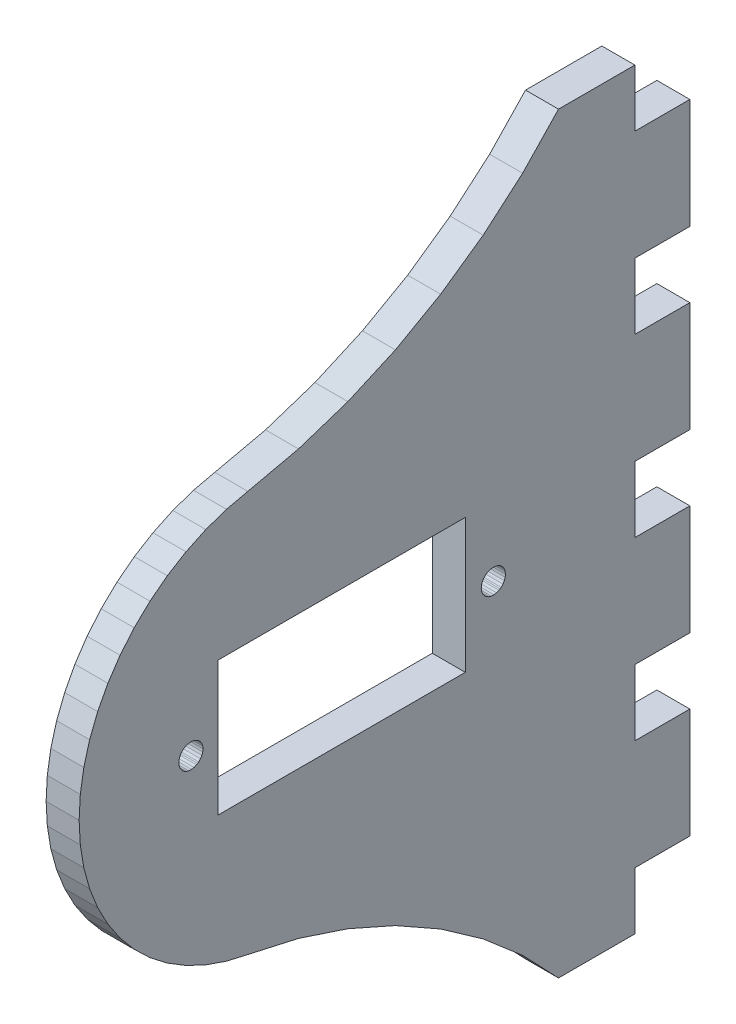
SolidWorks part; units mm, degrees
ref_plane "Front Plane" through (0, 0, 0) normal (0, 0, 1) x (1, 0, 0)
ref_plane "Top Plane" through (0, 0, 0) normal (0, 1, 0) x (1, 0, 0)
ref_plane "Right Plane" through (0, 0, 0) normal (1, 0, 0) x (0, 0, -1)
ref_plane "Plane1" through (3, 0, 0) normal (1, 0, 0) x (0, 0, -1)
sketch "Sketch1" plane through (3, 0, 0) normal (1, 0, 0) x (0, 0, -1)
  line L0 (-21.3207, 14.0362) -> (-22.7581, 12.6593)
  line L1 (-22.7581, 12.6593) -> (-24.0394, 11.136)
  line L2 (-24.0394, 11.136) -> (-25.1497, 9.4839)
  line L3 (-25.1497, 9.4839) -> (-26.0762, 7.7222)
  line L4 (-26.0762, 7.7222) -> (-26.8081, 5.8712)
  line L5 (-26.8081, 5.8712) -> (-27.3371, 3.9522)
  line L6 (-27.3371, 3.9522) -> (-27.6569, 1.9876)
  line L7 (-27.6569, 1.9876) -> (-27.7639, 0)
  line L8 (-27.7639, 0) -> (-27.6569, -1.9876)
  line L9 (-27.6569, -1.9876) -> (-27.3371, -3.9522)
  line L10 (-27.3371, -3.9522) -> (-26.8081, -5.8712)
  line L11 (-26.8081, -5.8712) -> (-26.0762, -7.7222)
  line L12 (-26.0762, -7.7222) -> (-25.1497, -9.4839)
  line L13 (-25.1497, -9.4839) -> (-24.0394, -11.136)
  line L14 (-24.0394, -11.136) -> (-22.7581, -12.6593)
  line L15 (-22.7581, -12.6593) -> (-21.3207, -14.0362)
  line L16 (-21.3207, -14.0362) -> (-19.7437, -15.2508)
  line L17 (-19.7437, -15.2508) -> (-18.0454, -16.289)
  line L18 (-18.0454, -16.289) -> (-16.2454, -17.1388)
  line L19 (-16.2454, -17.1388) -> (-14.3646, -17.7905)
  line L20 (-14.3646, -17.7905) -> (-12.4247, -18.2364)
  line L21 (-12.4247, -18.2364) -> (-7.8143, -19.2726)
  line L22 (-7.8143, -19.2726) -> (-3.3272, -20.7541)
  line L23 (-3.3272, -20.7541) -> (0.9938, -22.6669)
  line L24 (0.9938, -22.6669) -> (5.1073, -24.9927)
  line L25 (5.1073, -24.9927) -> (8.9739, -27.7091)
  line L26 (8.9739, -27.7091) -> (12.5566, -30.7902)
  line L27 (12.5566, -30.7902) -> (15.8213, -34.2066)
  line L28 (15.8213, -34.2066) -> (22.7639, -34.2066)
  line L29 (22.7639, -34.2066) -> (22.7639, -28.9999)
  line L30 (22.7639, -28.9999) -> (27.7639, -28.9999)
  line L31 (27.7639, -28.9999) -> (27.7639, -18.9999)
  line L32 (27.7639, -18.9999) -> (22.7639, -18.9999)
  line L33 (22.7639, -18.9999) -> (22.7639, -12.9999)
  line L34 (22.7639, -12.9999) -> (27.7639, -12.9999)
  line L35 (27.7639, -12.9999) -> (27.7639, -2.9999)
  line L36 (27.7639, -2.9999) -> (22.7639, -2.9999)
  line L37 (22.7639, -2.9999) -> (22.7639, 3.0001)
  line L38 (22.7639, 3.0001) -> (27.7639, 3.0001)
  line L39 (27.7639, 3.0001) -> (27.7639, 13.0001)
  line L40 (27.7639, 13.0001) -> (22.7639, 13.0001)
  line L41 (22.7639, 13.0001) -> (22.7639, 19.0001)
  line L42 (22.7639, 19.0001) -> (27.7639, 19.0001)
  line L43 (27.7639, 19.0001) -> (27.7639, 29.0001)
  line L44 (27.7639, 29.0001) -> (22.7639, 29.0001)
  line L45 (22.7639, 29.0001) -> (22.7639, 34.2066)
  line L46 (22.7639, 34.2066) -> (15.8213, 34.2066)
  line L47 (15.8213, 34.2066) -> (12.5566, 30.7902)
  line L48 (12.5566, 30.7902) -> (8.9739, 27.7091)
  line L49 (8.9739, 27.7091) -> (5.1073, 24.9927)
  line L50 (5.1073, 24.9927) -> (0.9938, 22.6669)
  line L51 (0.9938, 22.6669) -> (-3.3272, 20.7541)
  line L52 (-3.3272, 20.7541) -> (-7.8143, 19.2726)
  line L53 (-7.8143, 19.2726) -> (-12.4247, 18.2364)
  line L54 (-12.4247, 18.2364) -> (-14.3646, 17.7905)
  line L55 (-14.3646, 17.7905) -> (-16.2454, 17.1388)
  line L56 (-16.2454, 17.1388) -> (-18.0454, 16.289)
  line L57 (-18.0454, 16.289) -> (-19.7437, 15.2508)
  line L58 (-19.7437, 15.2508) -> (-21.3207, 14.0362)
  line L59 (7.3461, -5.9) -> (-15.1539, -5.9)
  line L60 (-15.1539, -5.9) -> (-15.1539, 6.3)
  line L61 (-15.1539, 6.3) -> (7.3461, 6.3)
  line L62 (7.3461, 6.3) -> (7.3461, -5.9)
  line L63 (-18.1192, 0.9719) -> (-17.8982, 1.0599)
  line L64 (-17.8982, 1.0599) -> (-17.6635, 1.0984)
  line L65 (-17.6635, 1.0984) -> (-17.426, 1.0855)
  line L66 (-17.426, 1.0855) -> (-17.1968, 1.0219)
  line L67 (-17.1968, 1.0219) -> (-16.9866, 0.9105)
  line L68 (-16.9866, 0.9105) -> (-16.8918, 0.8384)
  line L69 (-16.8918, 0.8384) -> (-16.7282, 0.6657)
  line L70 (-16.7282, 0.6657) -> (-16.6056, 0.4619)
  line L71 (-16.6056, 0.4619) -> (-16.5296, 0.2365)
  line L72 (-16.5296, 0.2365) -> (-16.5039, 0)
  line L73 (-16.5039, 0) -> (-16.5296, -0.2365)
  line L74 (-16.5296, -0.2365) -> (-16.6056, -0.4619)
  line L75 (-16.6056, -0.4619) -> (-16.7282, -0.6657)
  line L76 (-16.7282, -0.6657) -> (-16.8918, -0.8384)
  line L77 (-16.8918, -0.8384) -> (-16.9866, -0.9105)
  line L78 (-16.9866, -0.9105) -> (-17.0887, -0.9719)
  line L79 (-17.0887, -0.9719) -> (-17.3096, -1.0599)
  line L80 (-17.3096, -1.0599) -> (-17.5444, -1.0984)
  line L81 (-17.5444, -1.0984) -> (-17.7819, -1.0855)
  line L82 (-17.7819, -1.0855) -> (-18.0111, -1.0219)
  line L83 (-18.0111, -1.0219) -> (-18.2212, -0.9105)
  line L84 (-18.2212, -0.9105) -> (-18.4025, -0.7565)
  line L85 (-18.4025, -0.7565) -> (-18.5465, -0.5671)
  line L86 (-18.5465, -0.5671) -> (-18.6464, -0.3512)
  line L87 (-18.6464, -0.3512) -> (-18.6975, -0.1189)
  line L88 (-18.6975, -0.1189) -> (-18.7039, 0)
  line L89 (-18.7039, 0) -> (-18.6782, 0.2365)
  line L90 (-18.6782, 0.2365) -> (-18.6023, 0.4619)
  line L91 (-18.6023, 0.4619) -> (-18.4796, 0.6657)
  line L92 (-18.4796, 0.6657) -> (-18.3161, 0.8384)
  line L93 (-18.3161, 0.8384) -> (-18.1192, 0.9719)
  line L94 (9.3808, 0.9719) -> (9.6018, 1.0599)
  line L95 (9.6018, 1.0599) -> (9.8365, 1.0984)
  line L96 (9.8365, 1.0984) -> (10.074, 1.0855)
  line L97 (10.074, 1.0855) -> (10.3032, 1.0219)
  line L98 (10.3032, 1.0219) -> (10.5134, 0.9105)
  line L99 (10.5134, 0.9105) -> (10.6082, 0.8384)
  line L100 (10.6082, 0.8384) -> (10.7718, 0.6657)
  line L101 (10.7718, 0.6657) -> (10.8944, 0.4619)
  line L102 (10.8944, 0.4619) -> (10.9704, 0.2365)
  line L103 (10.9704, 0.2365) -> (10.9961, 0)
  line L104 (10.9961, 0) -> (10.9704, -0.2365)
  line L105 (10.9704, -0.2365) -> (10.8944, -0.4619)
  line L106 (10.8944, -0.4619) -> (10.7718, -0.6657)
  line L107 (10.7718, -0.6657) -> (10.6082, -0.8384)
  line L108 (10.6082, -0.8384) -> (10.5134, -0.9105)
  line L109 (10.5134, -0.9105) -> (10.4113, -0.9719)
  line L110 (10.4113, -0.9719) -> (10.1904, -1.0599)
  line L111 (10.1904, -1.0599) -> (9.9556, -1.0984)
  line L112 (9.9556, -1.0984) -> (9.7181, -1.0855)
  line L113 (9.7181, -1.0855) -> (9.4889, -1.0219)
  line L114 (9.4889, -1.0219) -> (9.2788, -0.9105)
  line L115 (9.2788, -0.9105) -> (9.0975, -0.7565)
  line L116 (9.0975, -0.7565) -> (8.9535, -0.5671)
  line L117 (8.9535, -0.5671) -> (8.8537, -0.3512)
  line L118 (8.8537, -0.3512) -> (8.8025, -0.1189)
  line L119 (8.8025, -0.1189) -> (8.7961, 0)
  line L120 (8.7961, 0) -> (8.8218, 0.2365)
  line L121 (8.8218, 0.2365) -> (8.8977, 0.4619)
  line L122 (8.8977, 0.4619) -> (9.0204, 0.6657)
  line L123 (9.0204, 0.6657) -> (9.1839, 0.8384)
  line L124 (9.1839, 0.8384) -> (9.3808, 0.9719)
extrude "Boss-Extrude1" add sketch "Sketch1" against normal blind 3
